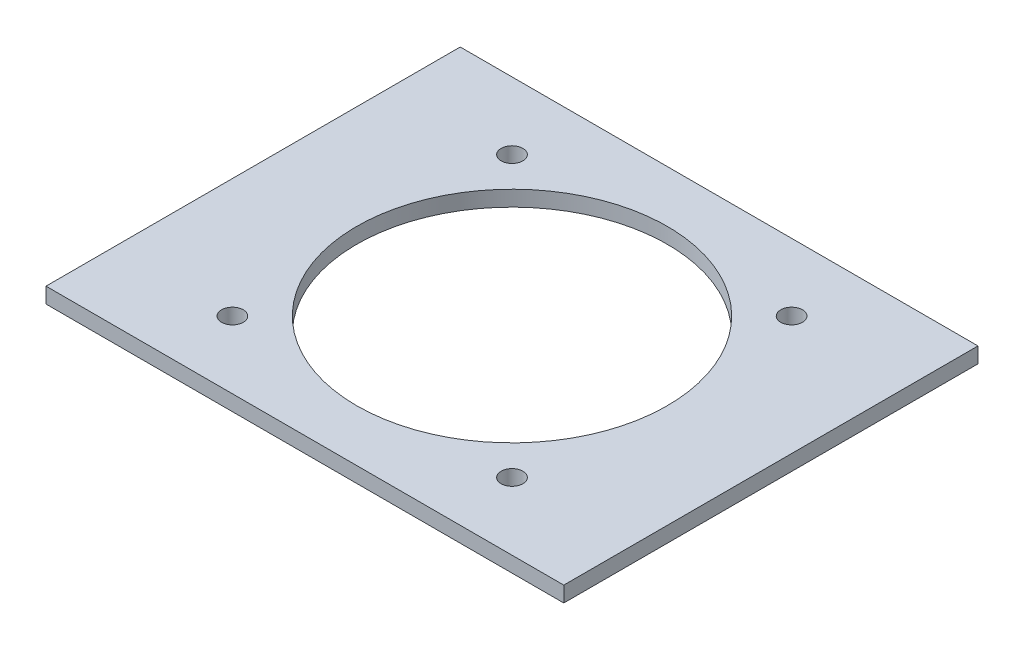
SolidWorks part; units mm, degrees
material "6061-T6 (SS)"
ref_plane "前视基准面" through (0, 0, 0) normal (0, 0, 1) x (1, 0, 0)
ref_plane "上视基准面" through (0, 0, 0) normal (0, 1, 0) x (1, 0, 0)
ref_plane "右视基准面" through (0, 0, 0) normal (1, 0, 0) x (0, 0, -1)
sketch "草图1" plane through (0, 0, 0) normal (0, 1, 0) x (1, 0, 0)
  line L1 (-50, 40) -> (50, 40)
  line L2 (-50, 40) -> (-50, -40)
  line L3 (-50, -40) -> (50, -40)
  line L4 (50, 40) -> (50, -40)
  line L5 (-50, 40) -> (50, -40) construction
  line L6 (-50, -40) -> (50, 40) construction
  circle A0 centre (0, 0) radius 30
  point P0 (0, 0)
  dimension "D3" = 60
  dimension "D1" = 80
  dimension "D2" = 100
extrude "凸台-拉伸1" add sketch "草图1" along normal blind 3
sketch "草图2" plane through (0, 3, 0) normal (0, 1, 0) x (1, 0, 0)
  circle A0 centre (27, 27) radius 2.1
  dimension "D1" = 4.2
extrude "切除-拉伸1" cut sketch "草图2" against normal blind 10
pattern_circular "阵列(圆周)1" count 4 over 360 about axis through (0, 0, 0) along (0, 1, 0) of "切除-拉伸1"
